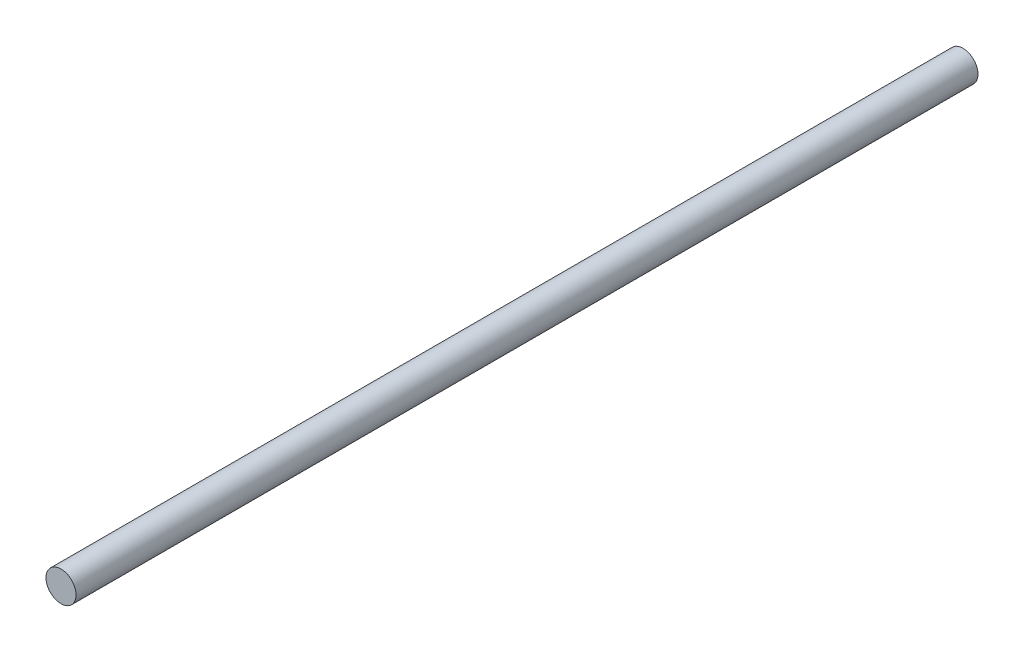
SolidWorks part; units mm, degrees
ref_plane "Front Plane" through (0, 0, 0) normal (0, 0, 1) x (1, 0, 0)
ref_plane "Top Plane" through (0, 0, 0) normal (0, 1, 0) x (1, 0, 0)
ref_plane "Right Plane" through (0, 0, 0) normal (1, 0, 0) x (0, 0, -1)
sketch "Sketch1" plane through (0, 0, 0) normal (0, 0, 1) x (1, 0, 0)
  circle A0 centre (0, 0) radius 1
extrude "Boss-Extrude1" add sketch "Sketch1" along normal blind 60
